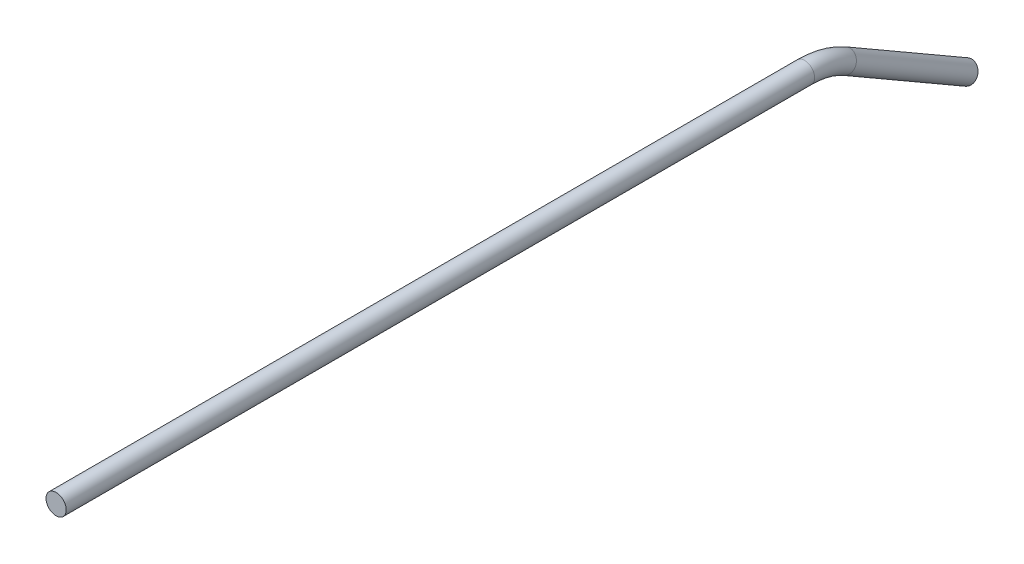
SolidWorks part; units mm, degrees
ref_plane "Front Plane" through (0, 0, 0) normal (0, 0, 1) x (1, 0, 0)
ref_plane "Top Plane" through (0, 0, 0) normal (0, 1, 0) x (1, 0, 0)
ref_plane "Right Plane" through (0, 0, 0) normal (1, 0, 0) x (0, 0, -1)
sketch "Sketch2" plane through (0, 0, 0) normal (0, 0, 1) x (1, 0, 0)
  circle A0 centre (0, 0) radius 3.175
  dimension "D1" = 6.35
sketch "Sketch4" plane through (0, 0, 0) normal (1, 0, 0) x (0, 0, -1)
  line L0 (0, 0) -> (234.4941, 0)
  line L1 (247.1941, -3.403) -> (285.2941, -25.4)
  arc A0 (247.1941, -3.403) -> (234.4941, 0) centre (234.4941, -25.4) ccw
  point P6 (241.3, 0)
  dimension "D4" = 25.4
  dimension "D1" = 241.3
  dimension "D2" = 50.8
  dimension "D3" = 30
sweep "Sweep1" add profiles "Sketch2" path "Sketch4"
